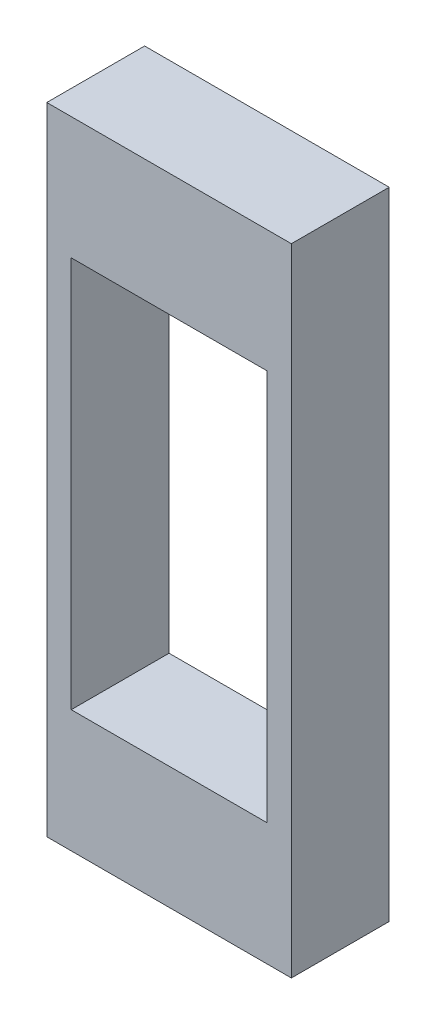
SolidWorks part; units mm, degrees
ref_plane "Front Plane" through (0, 0, 0) normal (0, 0, 1) x (1, 0, 0)
ref_plane "Top Plane" through (0, 0, 0) normal (0, 1, 0) x (1, 0, 0)
ref_plane "Right Plane" through (0, 0, 0) normal (1, 0, 0) x (0, 0, -1)
sketch "Sketch1" plane through (0, 0, 0) normal (0, 0, 1) x (1, 0, 0)
  line L1 (10.16, 20.32) -> (-10.16, 20.32)
  line L2 (10.16, 20.32) -> (10.16, -20.32)
  line L3 (10.16, -20.32) -> (-10.16, -20.32)
  line L4 (-10.16, 20.32) -> (-10.16, -20.32)
  line L5 (10.16, 20.32) -> (-10.16, -20.32) construction
  line L6 (10.16, -20.32) -> (-10.16, 20.32) construction
  line L7 (12.7, 33.02) -> (-12.7, 33.02)
  line L8 (12.7, 33.02) -> (12.7, -33.02)
  line L9 (12.7, -33.02) -> (-12.7, -33.02)
  line L10 (-12.7, 33.02) -> (-12.7, -33.02)
  line L11 (12.7, 33.02) -> (-12.7, -33.02) construction
  line L12 (12.7, -33.02) -> (-12.7, 33.02) construction
  point P0 (0, 0)
  point P6 (0, 0)
extrude "Boss-Extrude1" add sketch "Sketch1" along normal blind 10.16
